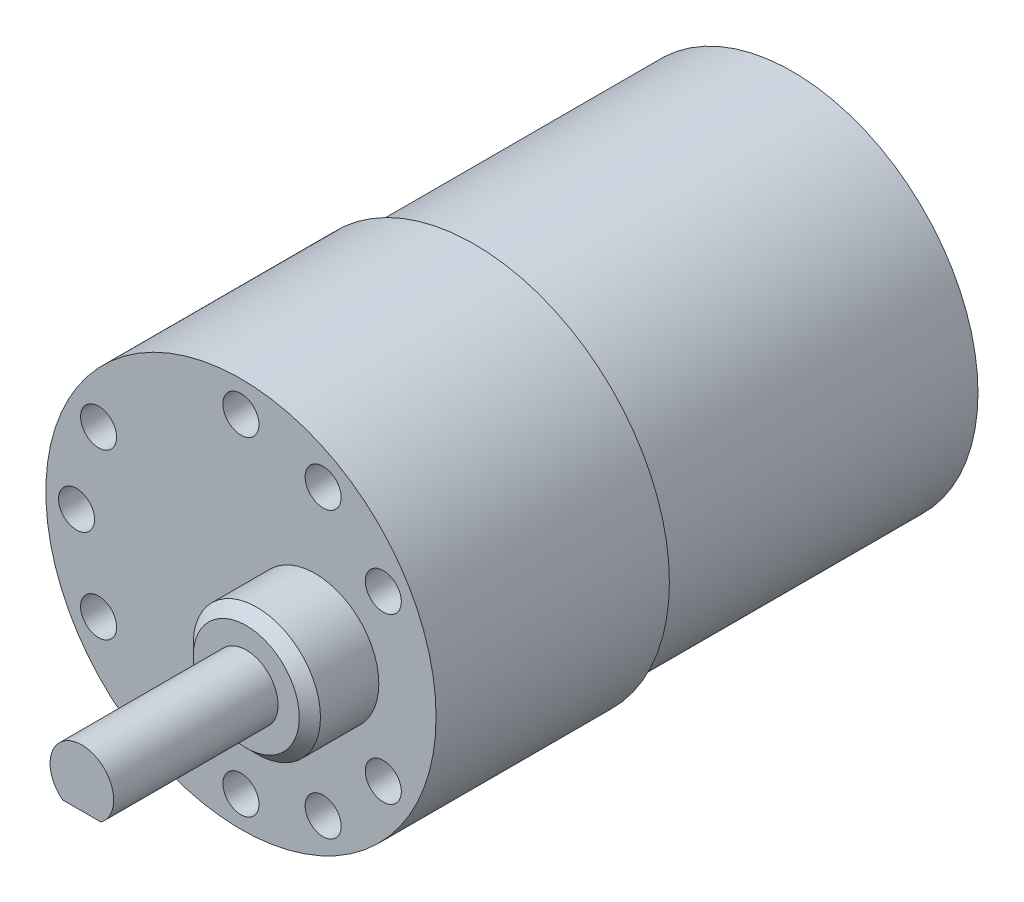
SolidWorks part; units mm, degrees
ref_plane "Front" through (0, 0, 0) normal (0, 0, 1) x (1, 0, 0)
ref_plane "Top" through (0, 0, 0) normal (0, 1, 0) x (1, 0, 0)
ref_plane "Right" through (0, 0, 0) normal (1, 0, 0) x (0, 0, -1)
sketch "Sketch1" plane through (0, 0, 0) normal (0, 0, 1) x (1, 0, 0)
  circle A0 centre (0, 0) radius 18.4
  dimension "D1" = 36.8
extrude "Boss-Extrude1" add sketch "Sketch1" along normal blind 22
sketch "Sketch2" plane through (0, 0, 0) normal (0, 0, -1) x (-1, 0, 0)
  circle A0 centre (0, 0) radius 17.5
  dimension "D1" = 35
extrude "Boss-Extrude2" add sketch "Sketch2" along normal blind 30
sketch "Sketch3" plane through (0, 0, 22) normal (0, 0, 1) x (1, 0, 0)
  line L0 (-18.4, 0) -> (18.4, 0) construction
  line L1 (0, 18.4) -> (0, -18.4) construction
  circle A0 centre (0, 0) radius 18.4 construction
  circle A1 centre (7, 0) radius 6
  dimension "D1" = 12
  dimension "D2" = 7
extrude "Boss-Extrude4" add sketch "Sketch3" along normal blind 6.5 contours A1
chamfer "Chamfer1" distance 1 angle 45 1 edges at (13, 0, 28.5)
sketch "Sketch4" plane through (0, 0, 28.5) normal (0, 0, 1) x (1, 0, 0)
  circle A0 centre (7, 0) radius 3
  dimension "D1" = 6
extrude "Boss-Extrude5" add sketch "Sketch4" along normal blind 3.5
sketch "Sketch5" plane through (0, 0, 32) normal (0, 0, 1) x (1, 0, 0)
  line L0 (5.2, -2.4) -> (8.8, -2.4)
  circle A0 centre (7, 0) radius 3
  circle M1 centre (7, 0) radius 3
  dimension "D2" = 6
  dimension "D1" = 2.4
extrude "Boss-Extrude6" add sketch "Sketch5" along normal blind 12 contours L0 M1
sketch "Sketch6" plane through (0, 0, 22) normal (0, 0, 1) x (1, 0, 0)
  circle A0 centre (0, 0) radius 15.5 construction
  circle A1 centre (0, 15.5) radius 1.7
  circle A2 centre (13.4234, 7.75) radius 1.7
  circle A3 centre (13.4234, -7.75) radius 1.7
  circle A4 centre (0, -15.5) radius 1.7
  circle A5 centre (-13.4234, -7.75) radius 1.7
  circle A6 centre (-13.4234, 7.75) radius 1.7
  circle A7 centre (-15.5, 0) radius 1.7
  circle A8 centre (7.75, 13.4234) radius 1.7
  circle A9 centre (7.75, -13.4234) radius 1.7
  point P17 (0, 0)
  point P25 (0, 0)
  dimension "D1" = 31
  dimension "D2" = 3.4
  dimension "D4" = 3.4
  dimension "D3" = 6
  dimension "D5" = 3
extrude "Cut-Extrude1" cut sketch "Sketch6" against normal blind 12
